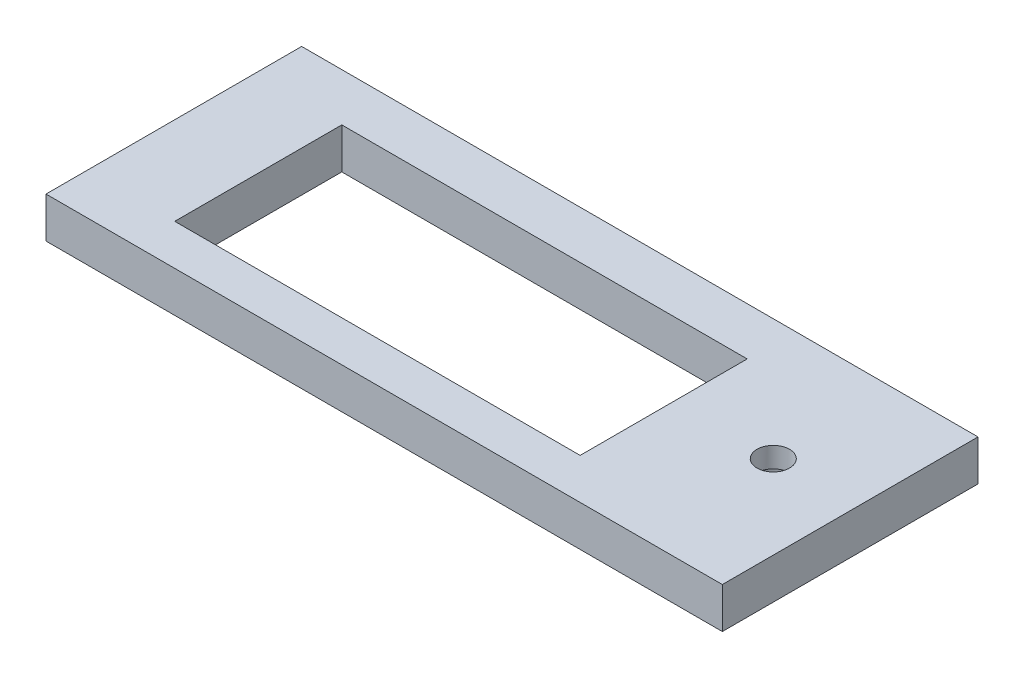
SolidWorks part; units mm, degrees
material "A286 Iron Base Superalloy"
ref_plane "Front Plane" through (0, 0, 0) normal (0, 0, 1) x (1, 0, 0)
ref_plane "Top Plane" through (0, 0, 0) normal (0, 1, 0) x (1, 0, 0)
ref_plane "Right Plane" through (0, 0, 0) normal (1, 0, 0) x (0, 0, -1)
sketch "Sketch2" plane through (0, 0, 0) normal (0, 1, 0) x (1, 0, 0)
  line L1 (-75, -31.375) -> (75, -31.375)
  line L2 (-75, -31.375) -> (-75, 31.375)
  line L3 (-75, 31.375) -> (75, 31.375)
  line L4 (75, -31.375) -> (75, 31.375)
  line L5 (-75, -31.375) -> (75, 31.375) construction
  line L6 (-75, 31.375) -> (75, -31.375) construction
  point P0 (0, 0)
  dimension "D1" = 150
  dimension "D2" = 62.75
extrude "Boss-Extrude1" add sketch "Sketch2" along normal blind 10
sketch "Sketch3" plane through (0, 10, 0) normal (0, 1, 0) x (1, 0, 0)
  line L0 (-75, 31.375) -> (-75, -31.375) construction
  line L1 (-61.4, -21.375) -> (38.1, -21.375)
  line L2 (-61.4, -21.375) -> (-61.4, 19.625)
  line L3 (-61.4, 19.625) -> (38.1, 19.625)
  line L4 (38.1, -21.375) -> (38.1, 19.625)
  line L5 (-61.4, -21.375) -> (38.1, 19.625) construction
  line L6 (-61.4, 19.625) -> (38.1, -21.375) construction
  line L7 (-75, -31.375) -> (75, -31.375) construction
  point P0 (-11.65, -0.875)
  dimension "D1" = 99.5
  dimension "D2" = 41
  dimension "D3" = 13.6
  dimension "D4" = 10
extrude "Cut-Extrude1" cut sketch "Sketch3" against normal through all
sketch "Sketch7" plane through (0, 0, 0) normal (0, -1, 0) x (1, 0, 0)
  line L0 (75, -31.375) -> (-75, -31.375) construction
  line L1 (8.6, -28.575) -> (-61.4, -28.575)
  line L2 (8.6, -28.575) -> (8.6, -24.575)
  line L3 (8.6, -24.575) -> (-61.4, -24.575)
  line L4 (-61.4, -28.575) -> (-61.4, -24.575)
  line L5 (-61.4, -19.625) -> (-61.4, 21.375) construction
  dimension "D1" = 2.8
  dimension "D2" = 4
  dimension "D3" = 0
  dimension "D4" = 70
extrude "Cut-Extrude4" cut sketch "Sketch7" against normal blind 7
sketch "Sketch8" plane through (0, 10, 0) normal (0, 1, 0) x (1, 0, 0)
  line L1 (75, -31.375) -> (75, 31.375) construction
  line L4 (-75, -31.375) -> (75, -31.375) construction
  circle A0 centre (62.5, 1.625) radius 4
  dimension "D1" = 8
  dimension "D2" = 33
  dimension "D3" = 12.5
extrude "Cut-Extrude5" cut sketch "Sketch8" against normal through all
sketch "Sketch9" plane through (0, 0, 0) normal (0, -1, 0) x (1, 0, 0)
  line L1 (75, 31.375) -> (75, -31.375) construction
  line L2 (-75, 31.375) -> (75, 31.375) construction
  circle A0 centre (61, -20.625) radius 6.5
  dimension "D1" = 13
  dimension "D2" = 52
  dimension "D3" = 14
extrude "Cut-Extrude6" cut sketch "Sketch9" against normal blind 7
sketch "Sketch10" plane through (0, 0, 0) normal (0, -1, 0) x (-1, 0, 0)
  line L1 (75, -31.375) -> (-75, -31.375) construction
  line L2 (-75, -31.375) -> (-75, 31.375) construction
  circle A0 centre (-62, -14.625) radius 3.5
  dimension "D5" = 7
  dimension "D1" = 16.75
  dimension "D2" = 13
extrude "Cut-Extrude7" cut sketch "Sketch10" against normal blind 7
sketch "Sketch11" plane through (0, 10, 0) normal (0, 1, 0) x (1, 0, 0)
  line L1 (-75, 31.375) -> (-83, 31.375)
  line L2 (-75, 31.375) -> (-75, -31.375)
  line L3 (-75, -31.375) -> (-83, -31.375)
  line L4 (-83, 31.375) -> (-83, -31.375)
  line L5 (75, 31.375) -> (83, 31.375)
  line L6 (75, 31.375) -> (75, -31.375)
  line L7 (75, -31.375) -> (83, -31.375)
  line L8 (83, 31.375) -> (83, -31.375)
  dimension "D1" = 8
  dimension "D2" = 8
extrude "Boss-Extrude2" add sketch "Sketch11" against normal through all
sketch "Sketch12" plane through (83, 0, 0) normal (1, 0, 0) x (0, 0, -1)
  line L0 (31.375, 0) -> (-20.3996, -51.7746)
  line L1 (-31.375, 0) -> (31.375, 0) construction
  dimension "D1" = 45
ref_plane "Plane1" through (0, -15.6875, -15.6875) normal (0, -0.7071, -0.7071) x (-1, 0, 0)
sketch "Sketch13" plane through (0, -15.6875, -15.6875) normal (0, -0.7071, -0.7071) x (-1, 0, 0)
  line L0 (-83, -22.1855) -> (-83, 22.1855) construction
  line L1 (-83, 22.1855) -> (83, 22.1855) construction
  circle A0 centre (-79, 10.2655) radius 1.5
  dimension "D3" = 3
  dimension "D1" = 4
  dimension "D2" = 11.92
hole_wizard "M3x0.5 Tapped Hole1" [suppressed] positions "Sketch17" profile "Sketch16" tap size "M3x0.5" standard "ANSI Metric"
sketch "Sketch17" plane through (0, -15.6875, -15.6875) normal (0, -0.7071, -0.7071) x (-1, 0, 0)
  point P0 (-79, 10.2655)
sketch "Sketch16" plane through (79, -8.4287, -22.9463) normal (1, 0, 0) x (0, 0.7071, -0.7071)
  line L0 (0, 0) -> (0, 20.7511)
  line L1 (0, 20.7511) -> (1.25, 20)
  line L2 (1.25, 20) -> (1.25, 0)
  line L5 (1.25, 0) -> (0, 0)
  line L10 (0, 20.7511) -> (-1.25, 20) construction
  line L11 (0, -6.35) -> (0, 107.95) construction
  dimension "Tap Drill Dia." = 2.5
  dimension "Tap Drill Depth" = 20
  dimension "Drill Angle" = 118
cosmetic thread "Hole Thread1" [suppressed] parameters "D1"=6, "D2"=3
sketch "Sketch18" plane through (83, 0, 0) normal (1, 0, 0) x (0, 0, -1)
  line L0 (-31.375, 0) -> (-5.7151, -25.6599)
  line L1 (-31.375, 0) -> (31.375, 0) construction
  dimension "D1" = 45
ref_plane "Plane2" through (0, -15.6875, 15.6875) normal (0, -0.7071, 0.7071) x (1, 0, 0)
sketch "Sketch19" plane through (0, -15.6875, 15.6875) normal (0, -0.7071, 0.7071) x (1, 0, 0)
  line L0 (83, 22.1855) -> (83, -14.1031) construction
  line L1 (-83, 22.1855) -> (83, 22.1855) construction
  circle A0 centre (79, 6.1255) radius 1.5
  dimension "D1" = 4
  dimension "D2" = 16.06
hole_wizard "M3x0.5 Tapped Hole2" positions "Sketch21" profile "Sketch20" tap size "M3x0.5" standard "ANSI Metric"
sketch "Sketch21" plane through (0, -15.6875, 15.6875) normal (0, -0.7071, 0.7071) x (1, 0, 0)
  point P0 (79, 6.1255)
sketch "Sketch20" plane through (79, -11.3561, 20.0189) normal (1, 0, 0) x (0, -0.7071, -0.7071)
  line L0 (0, 0) -> (0, 25.7511)
  line L1 (0, 25.7511) -> (1.25, 25)
  line L2 (1.25, 25) -> (1.25, 0)
  line L5 (1.25, 0) -> (0, 0)
  line L10 (0, 25.7511) -> (-1.25, 25) construction
  line L11 (0, -6.35) -> (0, 107.95) construction
  dimension "Tap Drill Dia." = 2.5
  dimension "Tap Drill Depth" = 25
  dimension "Drill Angle" = 118
cosmetic thread "Hole Thread2" parameters "D1"=6, "D2"=3
mirror "Mirror1" [suppressed] about plane through (0, 0, 0) normal (1, 0, 0)
sketch "Sketch23" plane through (-83, 0, 0) normal (-1, 0, 0) x (0, 0, 1)
  line L0 (31.375, 0) -> (-0.2899, -31.6649)
  line L1 (-31.375, 0) -> (31.375, 0) construction
  dimension "D1" = 45
ref_plane "Plane3" through (0, -15.6875, 15.6875) normal (0, -0.7071, 0.7071) x (-1, 0, 0)
sketch "Sketch24" plane through (0, -15.6875, 15.6875) normal (0, -0.7071, 0.7071) x (-1, 0, 0)
  line L0 (83, -22.1855) -> (-83, -22.1855) construction
  line L2 (83, 22.1855) -> (83, -22.1855) construction
  circle A0 centre (79, -12.1255) radius 3
  dimension "D1" = 10.06
  dimension "D2" = 4
hole_wizard "M3x0.5 Tapped Hole3" positions "Sketch26" profile "Sketch27" tap size "M3x0.5" standard "ANSI Metric"
sketch "Sketch26" plane through (0, -15.6875, 15.6875) normal (0, -0.7071, 0.7071) x (-1, 0, 0)
  point P0 (79, -12.1255)
sketch "Sketch27" plane through (-79, -7.1135, 24.2615) normal (1, 0, 0) x (0, -0.7071, -0.7071)
  line L0 (0, 0) -> (0, 21.7511)
  line L1 (0, 21.7511) -> (1.25, 21)
  line L2 (1.25, 21) -> (1.25, 0)
  line L5 (1.25, 0) -> (0, 0)
  line L10 (0, 21.7511) -> (-1.25, 21) construction
  line L11 (0, -6.35) -> (0, 107.95) construction
  dimension "Tap Drill Dia." = 2.5
  dimension "Tap Drill Depth" = 21
  dimension "Drill Angle" = 118
cosmetic thread "Hole Thread3" parameters "D1"=6, "D2"=3
sketch "Sketch28" plane through (0, 0, 0) normal (0, -1, 0) x (1, 0, 0)
  line L0 (83, 31.375) -> (83, -31.375) construction
  line L1 (83, -31.375) -> (-83, -31.375) construction
  line L2 (-83, -31.375) -> (-83, 31.375) construction
  circle A0 centre (79, -21.375) radius 1.5
  circle A1 centre (-79, -21.375) radius 1.5
  dimension "D1" = 3
  dimension "D4" = 3
  dimension "D2" = 4
  dimension "D3" = 10
  dimension "D5" = 10
  dimension "D6" = 4
extrude "Cut-Extrude8" cut sketch "Sketch28" against normal blind 5.5
sketch "Sketch29" plane through (0, 0, 0) normal (0, -1, 0) x (1, 0, 0)
  circle A0 centre (62.5, -1.625) radius 8.8145
extrude "Cut-Extrude9" cut sketch "Sketch29" against normal blind 5
